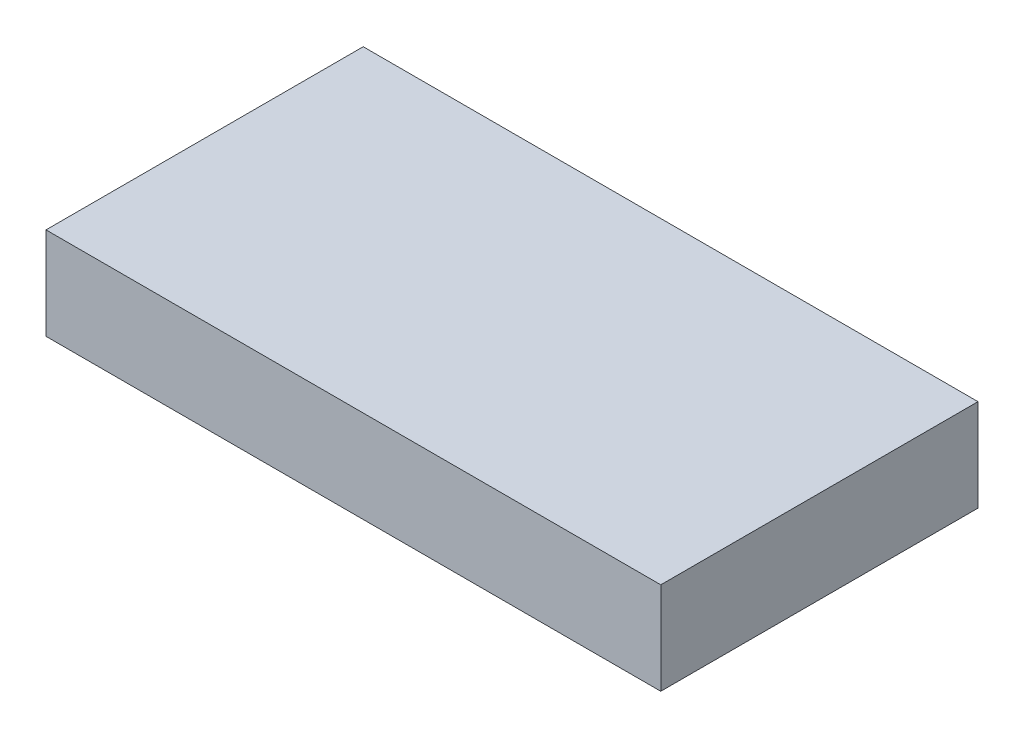
SolidWorks part; units mm, degrees
ref_plane "Alzado" through (0, 0, 0) normal (0, 0, 1) x (1, 0, 0)
ref_plane "Planta" through (0, 0, 0) normal (0, 1, 0) x (1, 0, 0)
ref_plane "Vista lateral" through (0, 0, 0) normal (1, 0, 0) x (0, 0, -1)
sketch "Croquis3" plane through (0, 0, 0) normal (0, 1, 0) x (1, 0, 0)
  line L1 (-25, 12.9) -> (25, 12.9)
  line L2 (-25, 12.9) -> (-25, -12.9)
  line L3 (-25, -12.9) -> (25, -12.9)
  line L4 (25, 12.9) -> (25, -12.9)
  line L5 (-25, 12.9) -> (25, -12.9) construction
  line L6 (-25, -12.9) -> (25, 12.9) construction
  point P0 (0, 0)
  dimension "D1" = 25.8
  dimension "D2" = 50
extrude "Saliente-Extruir3" add sketch "Croquis3" along normal mid plane 7.5
